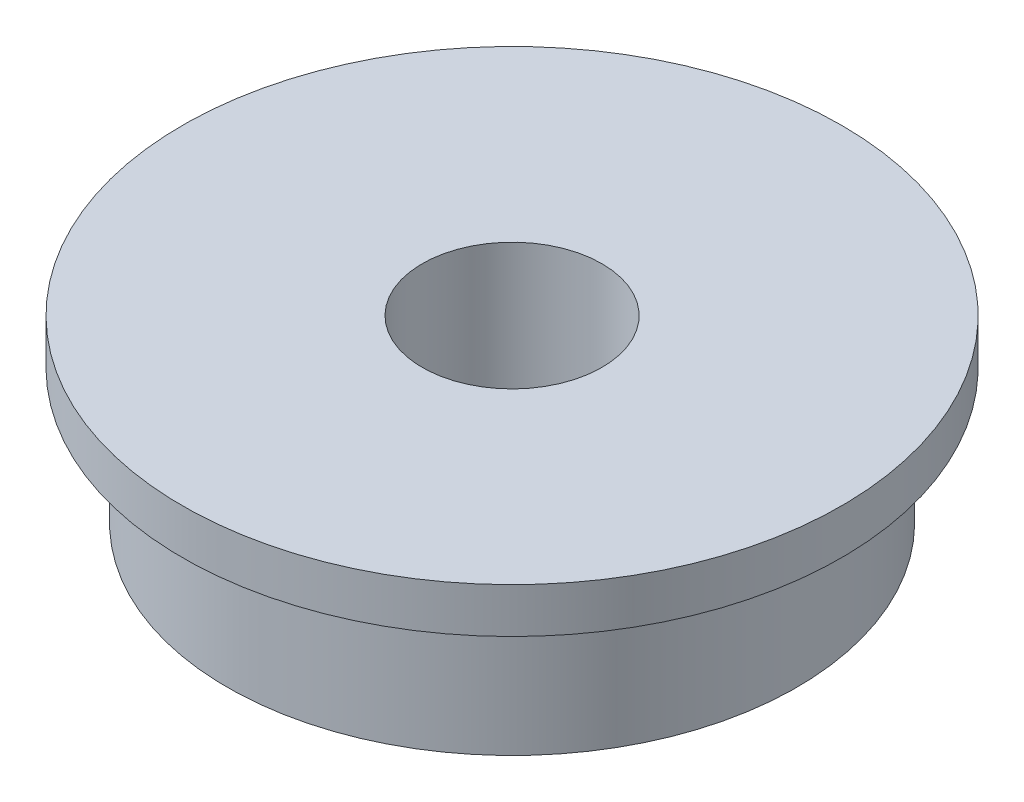
SolidWorks part; units mm, degrees
ref_plane "Front Plane" through (0, 0, 0) normal (0, 0, 1) x (1, 0, 0)
ref_plane "Top Plane" through (0, 0, 0) normal (0, 1, 0) x (1, 0, 0)
ref_plane "Right Plane" through (0, 0, 0) normal (1, 0, 0) x (0, 0, -1)
sketch "Sketch1" plane through (0, 0, 0) normal (0, 0, 1) x (1, 0, 0)
  line L0 (0, 0) -> (0, 6) construction
  line L1 (0, 6) -> (3, 6) construction
  line L2 (3, 6) -> (3, 0)
  line L3 (3, 0) -> (0, 0) construction
  line L4 (3, 6) -> (11, 6)
  line L5 (11, 6) -> (11, 4.5)
  line L6 (11, 4.5) -> (9.5, 4.5)
  line L7 (9.5, 4.5) -> (9.5, 0)
  line L8 (9.5, 0) -> (3, 0)
  dimension "D1" = 6
  dimension "D2" = 19
  dimension "D3" = 22
  dimension "D4" = 1.5
  dimension "D5" = 6
revolve "Revolve1" add sketch "Sketch1" angle 360 about L0
